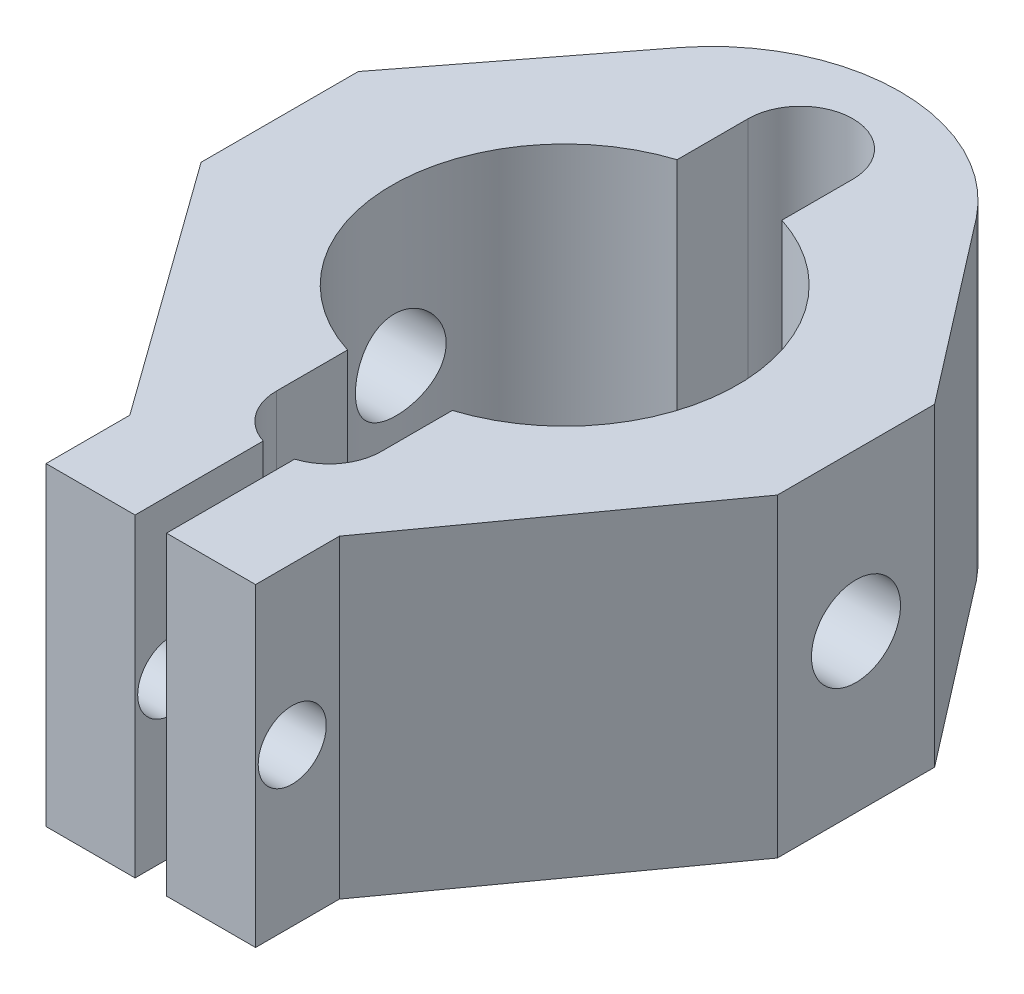
SolidWorks part; units mm, degrees
ref_plane "Front Plane" through (0, 0, 0) normal (0, 0, 1) x (1, 0, 0)
ref_plane "Top Plane" through (0, 0, 0) normal (0, 1, 0) x (1, 0, 0)
ref_plane "Right Plane" through (0, 0, 0) normal (1, 0, 0) x (0, 0, -1)
sketch "Sketch1" plane through (0, 0, 0) normal (0, 1, 0) x (1, 0, 0)
  line L0 (1.5, -35) -> (10, -35)
  line L1 (10, -35) -> (1.5, -35)
  line L2 (27.5, -2.7) -> (27.5, 12.3)
  line L4 (-27.5, -2.7) -> (-27.5, 12.3)
  line L5 (27.5, -2.7) -> (27.5, 12.3)
  line L6 (-10, -27) -> (-27.5, -2.7)
  line L7 (-1.5, -35) -> (-10, -35)
  line L8 (-10, -35) -> (-10, -27)
  line L9 (10, -35) -> (10, -27)
  line L10 (-27.5, -2.7) -> (-27.5, 12.3)
  line L11 (27.5, -2.7) -> (10, -27)
  line L12 (-5, 20.2242) -> (-5, 27)
  line L15 (27.5, 12.3) -> (14.0939, 29.6896)
  line L17 (-14.0939, 29.6896) -> (-27.5, 12.3)
  line L19 (-1.5, -35) -> (-10, -35)
  line L24 (5, -11.2242) -> (5, -18)
  line L26 (-1.5, -22.7697) -> (-1.5, -35)
  line L27 (5, 27) -> (5, 20.2242)
  line L31 (-5, -18) -> (-5, -11.2242)
  line L37 (1.5, -22.7697) -> (1.5, -35)
  arc A0 (-5, 20.2242) -> (-5, -11.2242) centre (0, 4.5) ccw
  arc A1 (5, -18) -> (1.5, -22.7697) centre (0, -18) cw
  arc A2 (5, 27) -> (-5, 27) centre (0, 27) ccw
  arc A3 (5, -11.2242) -> (5, 20.2242) centre (0, 4.5) ccw
  arc A4 (-14.0939, 29.6896) -> (14.0939, 29.6896) centre (0, 18.5113) cw
  arc A5 (-1.5, -22.7697) -> (-5, -18) centre (0, -18) cw
  point P0 (0, 0)
  dimension "D5" = 15
extrude "Boss-Extrude2" add sketch "Sketch1" along normal blind 30 contours L26 A5 L31 A0 L12 A2 L27 A3 L24 A1 L37 L0 L9 L11 L2 L15 A4 L17 L4 L6 L8 L7
sketch "Sketch2" plane through (-27.5, 0, 0) normal (-1, 0, 0) x (0, 0, 1)
  line L0 (2.7, 30) -> (-4.8, 30)
  line L1 (2.7, 30) -> (-12.3, 30) construction
  circle A0 centre (-4.8, 15) radius 4.25
extrude "Cut-Extrude1" cut sketch "Sketch2" against normal through all contours A0
sketch "Sketch5" plane through (-10, 0, 0) normal (-1, 0, 0) x (0, 0, 1)
  circle A0 centre (31.5, 15) radius 3.25
  dimension "D1" = 6.5
extrude "Cut-Extrude2" cut sketch "Sketch5" against normal blind 30 contours A0
